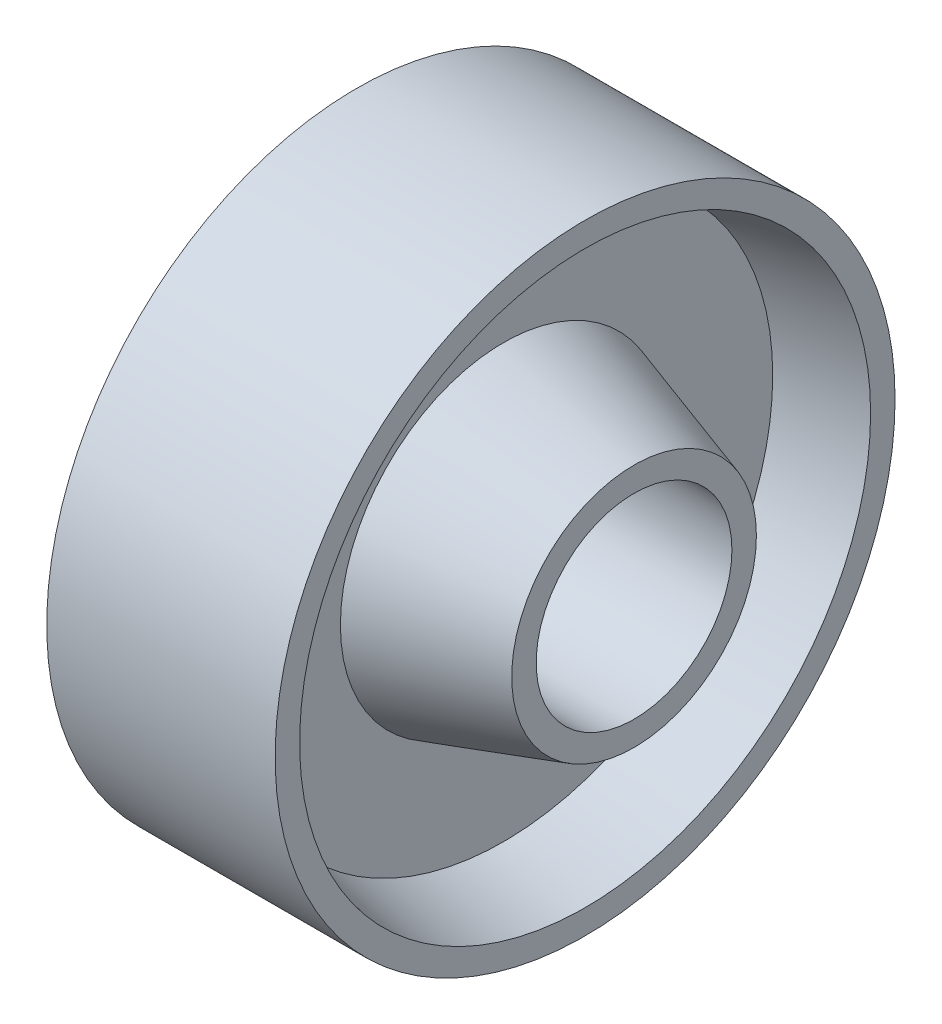
SolidWorks part; units mm, degrees
ref_plane "Front Plane" through (0, 0, 0) normal (0, 0, 1) x (1, 0, 0)
ref_plane "Top Plane" through (0, 0, 0) normal (0, 1, 0) x (1, 0, 0)
ref_plane "Right Plane" through (0, 0, 0) normal (1, 0, 0) x (0, 0, -1)
sketch "Sketch1" plane through (0, 0, 0) normal (0, 0, 1) x (1, 0, 0)
  line L0 (24.2799, 0) -> (0, 0) construction
  line L1 (0, 0) -> (0, 47.1254) construction
  line L2 (20, 12) -> (20, 15)
  line L3 (-20, 12) -> (-20, 15)
  line L4 (20, 15) -> (4, 20)
  line L5 (-20, 15) -> (-4, 20)
  line L6 (4, 20) -> (4, 33)
  line L7 (-4, 20) -> (-4, 33)
  line L8 (4, 33) -> (14, 35)
  line L9 (-4, 33) -> (-14, 35)
  line L10 (14, 35) -> (14, 38)
  line L11 (-14, 35) -> (-14, 38)
  line L12 (-14, 38) -> (14, 38)
  line L13 (20, 12) -> (-20, 12)
  dimension "D1" = 24
  dimension "D2" = 30
  dimension "D3" = 40
  dimension "D4" = 66
  dimension "D5" = 70
  dimension "D6" = 76
  dimension "D7" = 40
  dimension "D8" = 8
  dimension "D9" = 28
revolve "Revolve1" add sketch "Sketch1" angle 360 about L0
